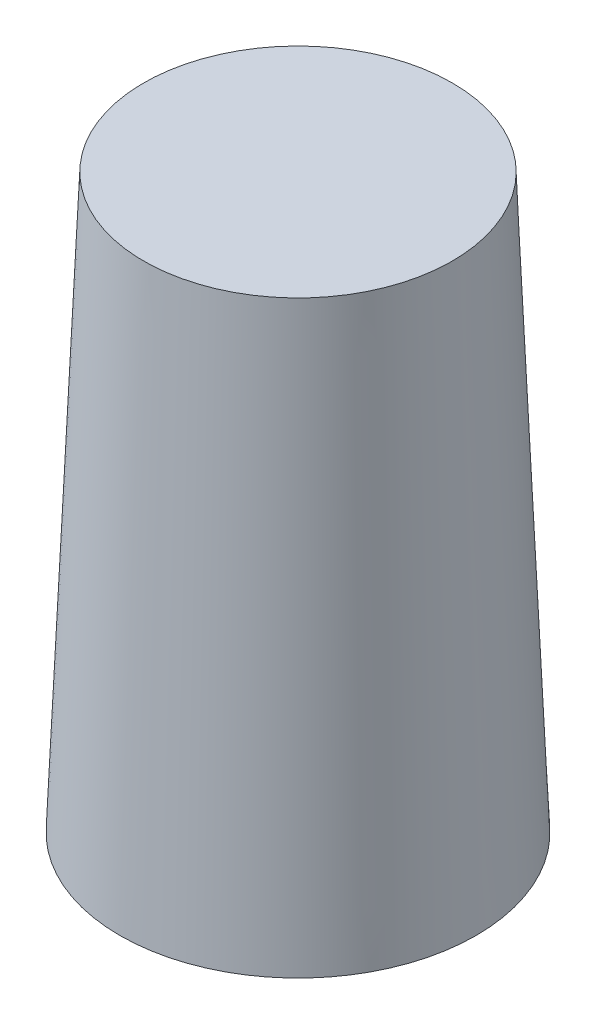
SolidWorks part; units mm, degrees
ref_plane "Front Plane" through (0, 0, 0) normal (0, 0, 1) x (1, 0, 0)
ref_plane "Top Plane" through (0, 0, 0) normal (0, 1, 0) x (1, 0, 0)
ref_plane "Right Plane" through (0, 0, 0) normal (1, 0, 0) x (0, 0, -1)
ref_axis "Axis1" through (0, -7.62, 0) along (0, 1, 0)
sketch "Sketch4" plane through (0, 0, 0) normal (0, 0, 1) x (1, 0, 0)
  line L0 (0, 0) -> (0, 2.54)
  line L1 (0, -7.62) -> (0, 160.02) construction
  line L2 (0, 152.4) -> (41.1, 152.4)
  line L3 (41.1, 152.4) -> (47.45, 0)
  line L4 (47.45, 0) -> (0, 0)
  line L5 (0, 149.86) -> (38.6636, 149.86)
  line L6 (38.6636, 149.86) -> (44.802, 2.54)
  line L7 (44.802, 2.54) -> (0, 2.54)
  line L9 (2.54, 2.54) -> (2.54, 149.86) construction
  line L10 (2.54, 149.86) -> (38.6636, 149.86) construction
  line L11 (44.802, 2.54) -> (2.54, 2.54) construction
  line L12 (0, 149.86) -> (0, 152.4)
  line L13 (0, 0) -> (0, 152.4) construction
  dimension "D1" = 152.4
  dimension "D2" = 41.1
  dimension "D3" = 47.45
  dimension "D4" = 2.54
revolve "Revolve1" add sketch "Sketch4" angle 360 about axis through (0, -7.62, 0) along (0, 1, 0)
ref_plane "Plane2" through (0, 152.4, 0) normal (0, 1, 0) x (1, 0, 0)
equation "\"S2_S_Airframe_ID\"= 3"
equation "\"S2_S_Airframe_Thickness\"= 0.11811"
equation "\"S2_B_Airframe_ID\"= 3.5"
equation "\"S2_B_Airframe_Thickness\"= 0.11811"
equation "\"S2_B_Airframe_Aft_Length\"= 30"
equation "\"S2_B_Airframe_Forward_Length\"= 3"
equation "\"S2_C_Coupler_Length\"= 6"
equation "\"S2_S_Airframe_Aft_Length\"= 32"
equation "\"S2_S_Airframe_Forward_Length\"= 16"
equation "\"D1@Sketch4\"=\"S2_C_Coupler_Length\""
equation "\"D2@Sketch4\"=(\"S2_S_Airframe_ID\")/2+\"S2_S_Airframe_Thickness\""
equation "\"D3@Sketch4\"=(\"S2_B_Airframe_ID\")/2+\"S2_B_Airframe_Thickness\""
